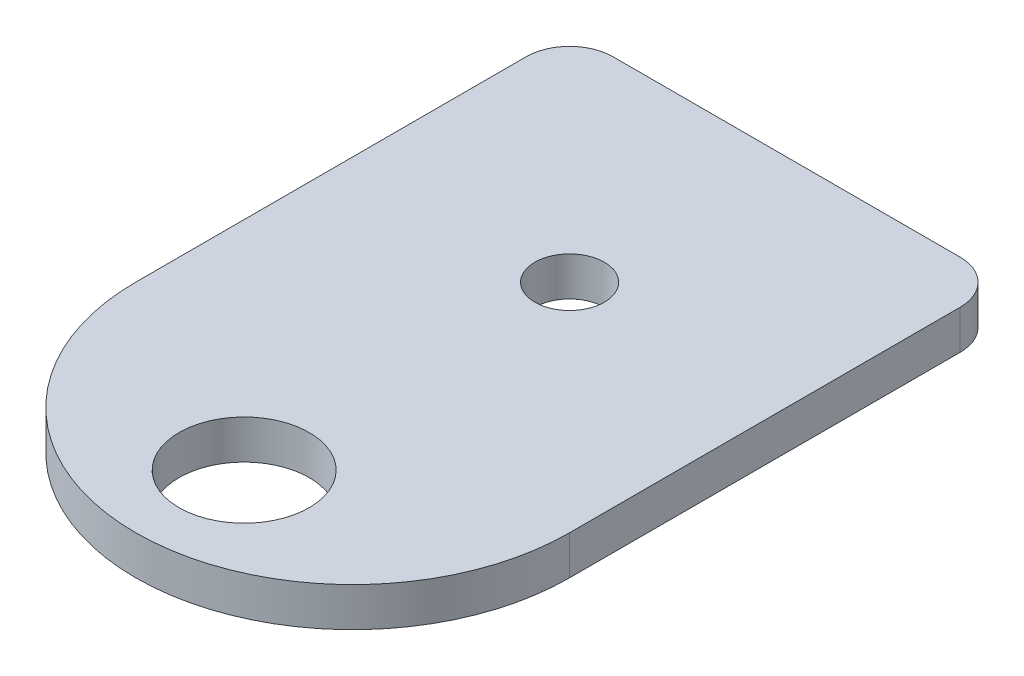
SolidWorks part; units mm, degrees
ref_plane "Front Plane" through (0, 0, 0) normal (0, 0, 1) x (1, 0, 0)
ref_plane "Top Plane" through (0, 0, 0) normal (0, 1, 0) x (1, 0, 0)
ref_plane "Right Plane" through (0, 0, 0) normal (1, 0, 0) x (0, 0, -1)
sketch "Sketch1" plane through (0, 0, 0) normal (0, 1, 0) x (1, 0, 0)
  line L1 (0, 0) -> (25.4, 0)
  line L2 (0, 0) -> (0, -25.4)
  line L3 (0, -25.4) -> (25.4, -25.4)
  line L4 (25.4, 0) -> (25.4, -25.4)
  circle A0 centre (12.7, -25.4) radius 12.7
  dimension "D1" = 25.4
  dimension "D2" = 25.4
extrude "Boss-Extrude1" add sketch "Sketch1" along normal blind 2.286 contours L3 A0 | L3 A0 | A0 L4 L1 L2
sketch "Sketch2" plane through (0, 2.286, 0) normal (0, 1, 0) x (1, 0, 0)
  line L0 (12.7, 0) -> (12.7, -12.7)
  line L1 (0, 0) -> (25.4, 0) construction
  line L2 (0, -25.4) -> (25.4, -25.4)
  line L3 (25.4, -25.4) -> (12.7, -25.4)
  line L4 (12.7, -25.4) -> (12.7, -38.1)
  circle A0 centre (12.7, -12.7) radius 2.032
  arc A1 (0, -25.4) -> (25.4, -25.4) centre (12.7, -25.4) ccw construction
  circle A2 centre (12.7, -31.75) radius 3.81
  dimension "D2" = 4.064
  dimension "D3" = 7.62
  dimension "D1" = 12.7
extrude "Cut-Extrude1" cut sketch "Sketch2" against normal through all and the other way through all
fillet "Fillet1" radius 2.54 1 edges at (0, 1.143, 0)
fillet "Fillet2" radius 2.54 1 edges at (25.4, 1.143, 0)
